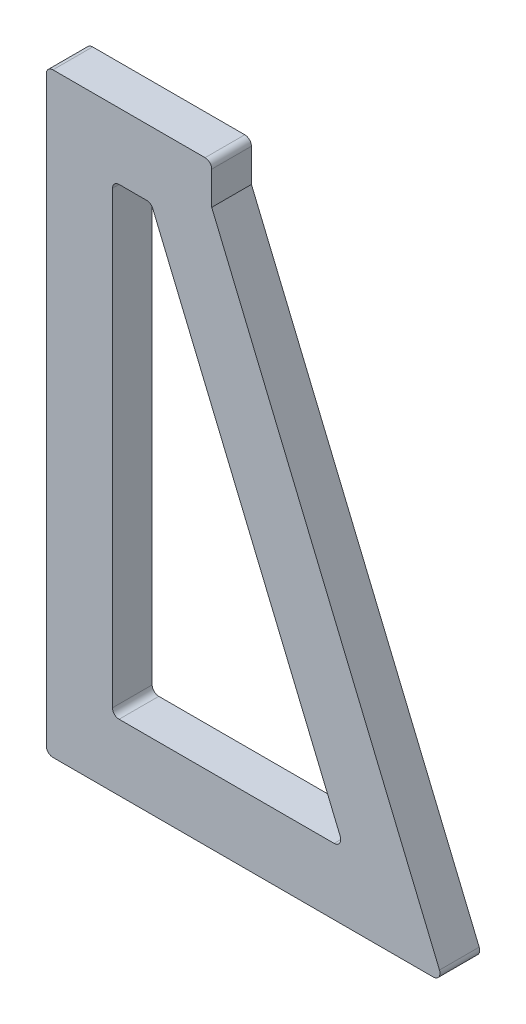
SolidWorks part; units mm, degrees
ref_plane "Plan de face" through (0, 0, 0) normal (0, 0, 1) x (1, 0, 0)
ref_plane "Plan de dessus" through (0, 0, 0) normal (0, 1, 0) x (1, 0, 0)
ref_plane "Plan de droite" through (0, 0, 0) normal (1, 0, 0) x (0, 0, -1)
sketch "Esquisse1" plane through (0, 0, 0) normal (0, 0, 1) x (1, 0, 0)
  line L0 (0, 1) -> (0, 89)
  line L1 (1, 90) -> (24, 90)
  line L2 (25, 89) -> (25, 84)
  line L3 (25, 84) -> (59.4231, 1.3846)
  line L4 (58.5, 0) -> (1, 0)
  line L5 (10, 11) -> (10, 79)
  line L6 (11, 80) -> (15.1667, 80)
  line L7 (16.0897, 79.3846) -> (44.4231, 11.3846)
  line L9 (43.5, 10) -> (11, 10)
  arc A0 (0, 1) -> (1, 0) centre (1, 1) ccw
  arc A1 (11, 10) -> (10, 11) centre (11, 11) cw
  arc A2 (16.0897, 79.3846) -> (15.1667, 80) centre (15.1667, 79) ccw
  arc A3 (11, 80) -> (10, 79) centre (11, 79) ccw
  arc A4 (0, 89) -> (1, 90) centre (1, 89) cw
  arc A5 (25, 89) -> (24, 90) centre (24, 89) ccw
  arc A6 (43.5, 10) -> (44.4231, 11.3846) centre (43.5, 11) ccw
  arc A7 (59.4231, 1.3846) -> (58.5, 0) centre (58.5, 1) cw
  point P12 (0, 0)
  point P15 (10, 10)
  point P20 (10, 80)
  point P23 (0, 90)
  point P26 (25, 90)
  point P29 (45, 10)
  point P32 (60, 0)
  dimension "D9" = 1
  dimension "D1" = 6
  dimension "D2" = 25
  dimension "D3" = 90
  dimension "D4" = 60
  dimension "D5" = 10
  dimension "D6" = 10
  dimension "D7" = 10
  dimension "D8" = 10
extrude "Boss.-Extru.1" add sketch "Esquisse1" along normal blind 6
